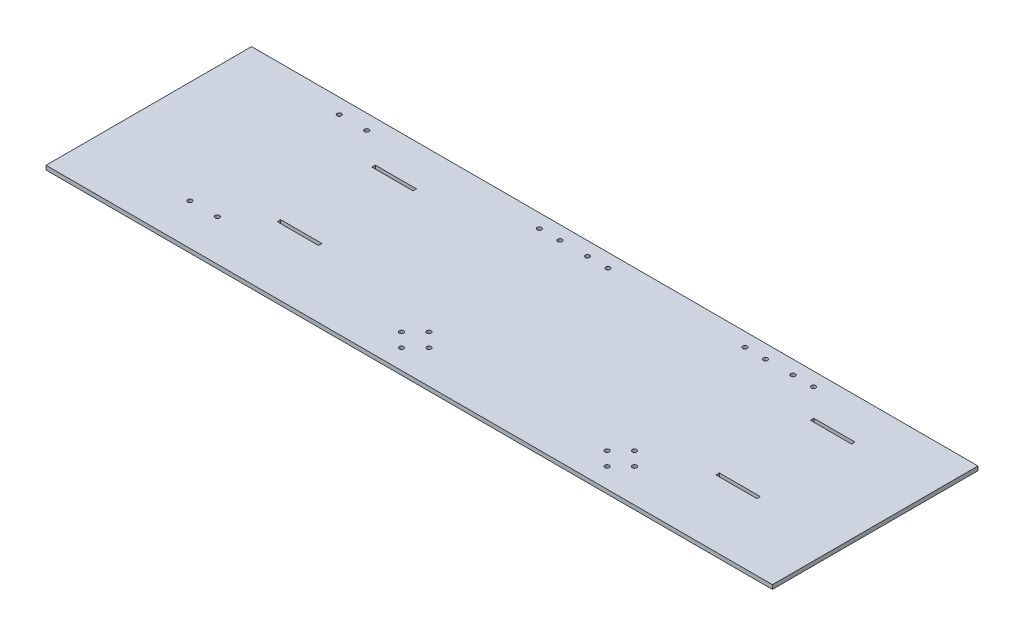
SolidWorks part; units mm, degrees
material "Thornel Mat VMA"
ref_plane "前视基准面" through (0, 0, 0) normal (0, 0, 1) x (1, 0, 0)
ref_plane "上视基准面" through (0, 0, 0) normal (0, 1, 0) x (1, 0, 0)
ref_plane "右视基准面" through (0, 0, 0) normal (1, 0, 0) x (0, 0, -1)
other "Configuration Table"
sketch "草图1" plane through (0, 0, 0) normal (0, 1, 0) x (1, 0, 0)
  line L0 (-223.1325, 65.7911) -> (246.8675, 65.7911) construction
  line L1 (-223.1325, 96.7911) -> (246.8675, 96.7911)
  line L2 (-223.1325, 96.7911) -> (-223.1325, -53.2089) construction
  line L3 (-223.1325, -53.2089) -> (246.8675, -53.2089)
  line L4 (246.8675, 96.7911) -> (246.8675, -53.2089)
  line L5 (-223.1325, -3.2089) -> (246.8675, -3.2089) construction
  line L6 (11.8675, 96.7911) -> (11.8675, -53.2089) construction
  line L7 (-163.1325, -1.9589) -> (-133.1325, -1.9589)
  line L8 (-163.1325, -1.9589) -> (-163.1325, -4.4589)
  line L9 (-163.1325, -4.4589) -> (-133.1325, -4.4589)
  line L10 (-133.1325, -1.9589) -> (-133.1325, -4.4589)
  line L11 (186.8675, -1.9589) -> (186.8675, -4.4589)
  line L12 (156.8675, -1.9589) -> (156.8675, -4.4589)
  line L13 (186.8675, -4.4589) -> (156.8675, -4.4589)
  line L14 (186.8675, -1.9589) -> (156.8675, -1.9589)
  line L15 (-209.769, 65.7911) -> (-209.769, -3.2089) construction
  line L16 (-209.769, 31.2911) -> (246.8675, 31.2911) construction
  line L17 (156.8675, 64.5411) -> (156.8675, 67.0411)
  line L18 (186.8675, 67.0411) -> (156.8675, 67.0411)
  line L19 (186.8675, 64.5411) -> (186.8675, 67.0411)
  line L20 (186.8675, 64.5411) -> (156.8675, 64.5411)
  line L21 (-163.1325, 67.0411) -> (-133.1325, 67.0411)
  line L22 (-133.1325, 64.5411) -> (-133.1325, 67.0411)
  line L23 (-163.1325, 64.5411) -> (-133.1325, 64.5411)
  line L24 (-163.1325, 64.5411) -> (-163.1325, 67.0411)
  line L25 (-148.1325, -4.4589) -> (-148.1325, -53.2089) construction
  line L26 (-223.1325, -53.2089) -> (-283.1325, -53.2089)
  line L28 (-223.1325, 96.7911) -> (-283.1325, 96.7911)
  line L29 (-283.1325, -53.2089) -> (-283.1325, 96.7911)
  line L30 (171.8675, -4.4589) -> (171.8675, -53.2089) construction
  line L31 (-188.1325, -23.2089) -> (-208.1325, -23.2089) construction
  line L32 (-148.1325, -28.8339) -> (11.8675, -28.8339) construction
  line L33 (171.8675, -28.8339) -> (11.8675, -28.8339) construction
  line L34 (-38.1325, -28.8339) -> (-38.1325, 96.7911) construction
  line L35 (111.8675, -28.8339) -> (111.8675, 96.7911) construction
  line L36 (-63.1325, 86.7911) -> (-48.1325, 86.7911) construction
  line L37 (86.8675, 86.7911) -> (101.8675, 86.7911) construction
  circle A0 centre (-208.1325, -23.2089) radius 1.6
  circle A1 centre (-188.1325, -23.2089) radius 1.6
  circle A2 centre (-208.1325, 85.7911) radius 1.6
  circle A3 centre (-188.1325, 85.7911) radius 1.6
  circle A4 centre (-38.1325, -28.8339) radius 10 construction
  circle A5 centre (111.8675, -28.8339) radius 10 construction
  circle A6 centre (-48.1325, -28.8339) radius 1.6
  circle A7 centre (-38.1325, -38.8339) radius 1.6
  circle A8 centre (-28.1325, -28.8339) radius 1.6
  circle A9 centre (-38.1325, -18.8339) radius 1.6
  circle A10 centre (101.8675, -28.8339) radius 1.6
  circle A11 centre (111.8675, -18.8339) radius 1.6
  circle A12 centre (121.8675, -28.8339) radius 1.6
  circle A13 centre (111.8675, -38.8339) radius 1.6
  circle A14 centre (-63.1325, 86.7911) radius 1.6
  circle A15 centre (-48.1325, 86.7911) radius 1.6
  circle A16 centre (-28.1325, 86.7911) radius 1.6
  circle A17 centre (-13.1325, 86.7911) radius 1.6
  circle A20 centre (86.8675, 86.7911) radius 1.6
  circle A21 centre (101.8675, 86.7911) radius 1.6
  circle A22 centre (136.8675, 86.7911) radius 1.6
  circle A23 centre (121.8675, 86.7911) radius 1.6
  point P12 (-163.1325, -3.2089)
  dimension "D9" = 3.2
  dimension "D13" = 150
  dimension "D15" = 20
  dimension "D16" = 3.2
  dimension "D17" = 3.2
  dimension "D21" = 3.2
  dimension "D1" = 470
  dimension "D2" = 150
  dimension "D3" = 69
  dimension "D4" = 50
  dimension "D5" = 60
  dimension "D6" = 2.5
  dimension "D7" = 30
  dimension "D8" = 60
  dimension "D10" = 20
  dimension "D11" = 20
  dimension "D12" = 15
  dimension "D14" = 50
  dimension "D18" = 15
  dimension "D19" = 10
  dimension "D20" = 10
  dimension "D22" = 10
  dimension "D23" = 15
  dimension "D24" = 10
  dimension "D25" = 109
  dimension "D26" = 11
extrude "凸台-拉伸1" add sketch "草图1" along normal blind 3
